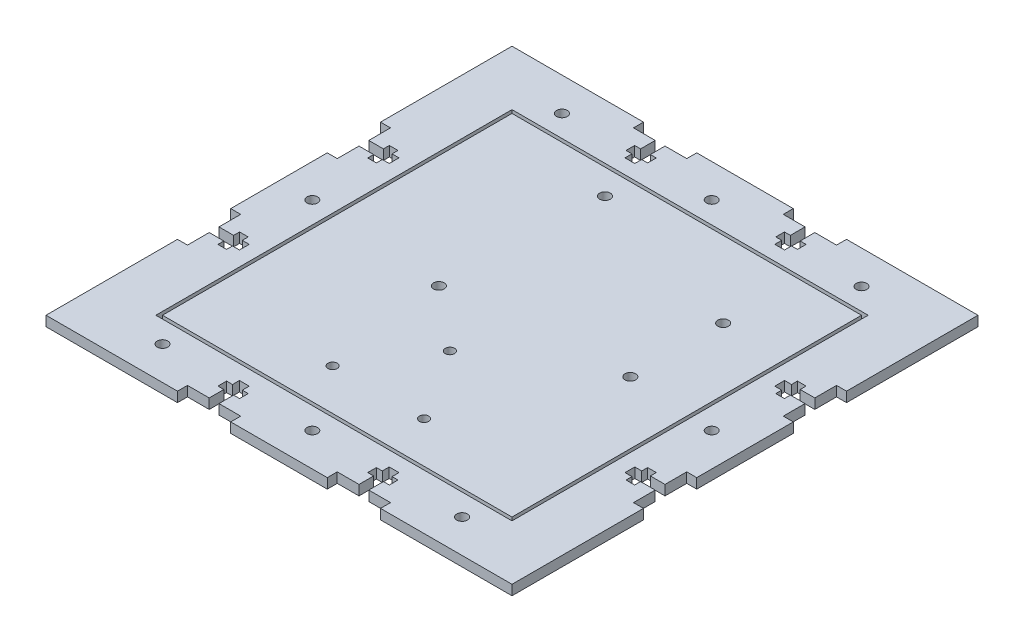
SolidWorks part; units mm, degrees
ref_plane "Front Plane" through (0, 0, 0) normal (0, 0, 1) x (1, 0, 0)
ref_plane "Top Plane" through (0, 0, 0) normal (0, 1, 0) x (1, 0, 0)
ref_plane "Right Plane" through (0, 0, 0) normal (1, 0, 0) x (0, 0, -1)
sketch "Sketch2" plane through (0, 0, 0) normal (0, 1, 0) x (1, 0, 0)
  line L0 (-70, 70) -> (70, -70) construction
  line L1 (-70, 70) -> (70, 70)
  line L2 (-70, 70) -> (-70, -70)
  line L3 (-70, -70) -> (70, -70)
  line L4 (70, 70) -> (70, -70)
  line L5 (70, 70) -> (-70, -70) construction
  line L6 (-0.0302, -29.4237) -> (-0.0302, -47.5058) construction
  line L7 (-50, 50) -> (50, -50) construction
  line L8 (50, 50) -> (-50, 50)
  line L9 (50, 50) -> (50, -50)
  line L10 (50, -50) -> (-50, -50)
  line L11 (-50, 50) -> (-50, -50)
  line L12 (50, 50) -> (-50, -50) construction
  line L13 (-18.6116, -3.3508) -> (-18.6116, 44.9492) construction
  line L14 (33.7884, 1.7492) -> (22.0917, 1.7492)
  line L15 (-18.6116, -3.3508) -> (22.0917, -3.3508)
  line L16 (22.0917, -3.3508) -> (22.0917, 1.7492)
  line L17 (0, 70) -> (0, -70) construction
  line L18 (-70, 0) -> (70, 0) construction
  line L19 (0, 70) -> (0, 50) construction
  line L20 (-50, 0) -> (-70, 0) construction
  line L21 (0, -50) -> (0, -70) construction
  line L22 (50, 0) -> (70, 0) construction
  line L23 (-45, 70) -> (-45, -70) construction
  line L24 (45, 70) -> (45, -70) construction
  line L25 (-45, 50) -> (-45, 70) construction
  line L26 (45, 50) -> (45, 70) construction
  line L27 (-45, -50) -> (-45, -70) construction
  line L28 (45, -50) -> (45, -70) construction
  circle A3 centre (-17.0116, 44.9492) radius 1.6
  circle A4 centre (-18.6116, -3.3508) radius 1.6
  circle A5 centre (33.7884, 29.6492) radius 1.6
  circle A6 centre (33.7884, 1.7492) radius 1.6
  circle A10 centre (0, 60) radius 1.6
  circle A11 centre (-60, 0) radius 1.6
  circle A12 centre (0, -60) radius 1.6
  circle A13 centre (60, 0) radius 1.6
  circle A14 centre (-45, 60) radius 1.6
  circle A15 centre (45, 60) radius 1.6
  circle A16 centre (-45, -60) radius 1.6
  circle A17 centre (45, -60) radius 1.6
  circle A18 centre (-0.0302, -18.6237) radius 1.4
  circle A19 centre (-13.7802, -40.1237) radius 1.4
  circle A20 centre (13.7198, -40.1237) radius 1.4
  point P12 (0, 0)
  point P18 (0, 0)
  point P40 (0, 60)
  point P44 (-60, 0)
  point P49 (0, -60)
  point P54 (60, 0)
  point P63 (-45, 60)
  point P68 (45, 60)
  point P73 (-45, -60)
  point P78 (45, -60)
  dimension "D3" = 25
  dimension "D9" = 3.2
  dimension "D11" = 2.8
  dimension "D1" = 140
  dimension "D2" = 100
  dimension "D4" = 50.8
  dimension "D5" = 27.9
  dimension "D6" = 5.1
  dimension "D7" = 48.3
  dimension "D8" = 40.7033
  dimension "D10" = 25
extrude "Boss-Extrude2" add sketch "Sketch2" along normal blind 3
sketch "Sketch3" plane through (0, 3, 0) normal (0, 1, 0) x (1, 0, 0)
  line L0 (-30.5, 70) -> (-30.5, 67)
  line L1 (-70, 70) -> (70, 70) construction
  line L2 (-30.5, 67) -> (-14.5, 67)
  line L3 (-14.5, 67) -> (-14.5, 70)
  line L4 (-14.5, 70) -> (-30.5, 70)
  line L6 (-1.65, 0) -> (1.65, 0) construction
  line L7 (-70, 70) -> (-70, -70) construction
  line L8 (-14.5, -67) -> (-14.5, -70)
  line L9 (-30.5, -67) -> (-14.5, -67)
  line L10 (-30.5, -70) -> (-30.5, -67)
  line L11 (-14.5, -70) -> (-30.5, -70)
  line L12 (0, -1.65) -> (0, 1.65) construction
  line L13 (30.5, -67) -> (14.5, -67)
  line L14 (30.5, -70) -> (30.5, -67)
  line L15 (14.5, -70) -> (30.5, -70)
  line L16 (14.5, -67) -> (14.5, -70)
  line L17 (14.5, 67) -> (14.5, 70)
  line L18 (30.5, 67) -> (14.5, 67)
  line L19 (30.5, 70) -> (30.5, 67)
  line L20 (14.5, 70) -> (30.5, 70)
  line L21 (-70, 30.5) -> (-67, 30.5)
  line L22 (-67, 30.5) -> (-67, 14.5)
  line L23 (-67, 14.5) -> (-70, 14.5)
  line L25 (-70, 14.5) -> (-70, 30.5)
  line L27 (67, 14.5) -> (70, 14.5)
  line L28 (67, 30.5) -> (67, 14.5)
  line L29 (70, 30.5) -> (67, 30.5)
  line L30 (70, 14.5) -> (70, 30.5)
  line L31 (67, -30.5) -> (67, -14.5)
  line L32 (70, -30.5) -> (67, -30.5)
  line L33 (70, -14.5) -> (70, -30.5)
  line L34 (67, -14.5) -> (70, -14.5)
  line L35 (-67, -14.5) -> (-70, -14.5)
  line L36 (-67, -30.5) -> (-67, -14.5)
  line L37 (-70, -30.5) -> (-67, -30.5)
  line L38 (-70, -14.5) -> (-70, -30.5)
  dimension "D3" = 39.5
  dimension "D1" = 3
  dimension "D2" = 16
  dimension "D4" = 3
  dimension "D5" = 16
  dimension "D6" = 39.5
extrude "Cut-Extrude2" cut sketch "Sketch3" against normal blind 3
sketch "Sketch4" plane through (0, 3, 0) normal (0, 1, 0) x (1, 0, 0)
  line L0 (-22.5, 67) -> (-22.5, -67) construction
  line L1 (-30.5, 67) -> (-14.5, 67) construction
  line L2 (-14.5, -67) -> (-30.5, -67) construction
  line L3 (-23.97, 67) -> (-23.97, 62.6)
  line L4 (-67, 22.5) -> (67, 22.5) construction
  line L5 (-67, 14.5) -> (-67, 30.5) construction
  line L6 (-23.97, 62.6) -> (-25.75, 62.6)
  line L7 (67, 30.5) -> (67, 14.5) construction
  line L9 (-25.75, 62.6) -> (-25.75, 60)
  line L10 (-25.75, 60) -> (-23.97, 60)
  line L11 (-23.97, 60) -> (-23.97, 57.92)
  line L12 (-23.97, 57.92) -> (-21.03, 57.92)
  line L14 (-21.03, 67) -> (-23.97, 67)
  line L15 (-21.03, 60) -> (-21.03, 57.92)
  line L16 (-19.25, 60) -> (-21.03, 60)
  line L17 (-19.25, 62.6) -> (-19.25, 60)
  line L18 (-21.03, 62.6) -> (-19.25, 62.6)
  line L19 (-21.03, 67) -> (-21.03, 62.6)
  line L20 (-1.65, 0) -> (1.65, 0) construction
  line L21 (-23.97, -62.6) -> (-25.75, -62.6)
  line L22 (-23.97, -67) -> (-23.97, -62.6)
  line L23 (-21.03, -67) -> (-23.97, -67)
  line L24 (-21.03, -67) -> (-21.03, -62.6)
  line L25 (-21.03, -62.6) -> (-19.25, -62.6)
  line L26 (-19.25, -62.6) -> (-19.25, -60)
  line L27 (-19.25, -60) -> (-21.03, -60)
  line L28 (-21.03, -60) -> (-21.03, -57.92)
  line L29 (-23.97, -57.92) -> (-21.03, -57.92)
  line L30 (-23.97, -60) -> (-23.97, -57.92)
  line L31 (-25.75, -60) -> (-23.97, -60)
  line L32 (-25.75, -62.6) -> (-25.75, -60)
  line L33 (0, -1.65) -> (0, 1.65) construction
  line L34 (21.03, -60) -> (21.03, -57.92)
  line L35 (21.03, -67) -> (23.97, -67)
  line L36 (23.97, -67) -> (23.97, -62.6)
  line L37 (23.97, -62.6) -> (25.75, -62.6)
  line L38 (25.75, -62.6) -> (25.75, -60)
  line L39 (25.75, -60) -> (23.97, -60)
  line L40 (23.97, -60) -> (23.97, -57.92)
  line L41 (23.97, -57.92) -> (21.03, -57.92)
  line L42 (19.25, -60) -> (21.03, -60)
  line L43 (19.25, -62.6) -> (19.25, -60)
  line L44 (21.03, -62.6) -> (19.25, -62.6)
  line L45 (21.03, -67) -> (21.03, -62.6)
  line L46 (21.03, 67) -> (23.97, 67)
  line L47 (21.03, 67) -> (21.03, 62.6)
  line L48 (21.03, 62.6) -> (19.25, 62.6)
  line L49 (23.97, 67) -> (23.97, 62.6)
  line L50 (23.97, 62.6) -> (25.75, 62.6)
  line L51 (25.75, 62.6) -> (25.75, 60)
  line L52 (25.75, 60) -> (23.97, 60)
  line L53 (23.97, 60) -> (23.97, 57.92)
  line L54 (23.97, 57.92) -> (21.03, 57.92)
  line L55 (21.03, 60) -> (21.03, 57.92)
  line L56 (19.25, 60) -> (21.03, 60)
  line L57 (19.25, 62.6) -> (19.25, 60)
  line L76 (67, 23.97) -> (62.6, 23.97)
  line L77 (62.6, 23.97) -> (62.6, 25.75)
  line L90 (67, 23.97) -> (67, 21.03)
  line L91 (67, 21.03) -> (62.6, 21.03)
  line L92 (62.6, 21.03) -> (62.6, 19.25)
  line L93 (62.6, 19.25) -> (60, 19.25)
  line L94 (60, 19.25) -> (60, 21.03)
  line L95 (60, 21.03) -> (57.92, 21.03)
  line L96 (57.92, 21.03) -> (57.92, 23.97)
  line L97 (62.6, 25.75) -> (60, 25.75)
  line L98 (60, 25.75) -> (60, 23.97)
  line L99 (60, 23.97) -> (57.92, 23.97)
  line L100 (-67, 23.97) -> (-67, 21.03)
  line L101 (-67, 23.97) -> (-62.6, 23.97)
  line L102 (-62.6, 23.97) -> (-62.6, 25.75)
  line L103 (-62.6, 25.75) -> (-60, 25.75)
  line L104 (-60, 25.75) -> (-60, 23.97)
  line L105 (-60, 23.97) -> (-57.92, 23.97)
  line L106 (-57.92, 21.03) -> (-57.92, 23.97)
  line L107 (-60, 21.03) -> (-57.92, 21.03)
  line L108 (-60, 19.25) -> (-60, 21.03)
  line L109 (-62.6, 19.25) -> (-60, 19.25)
  line L110 (-62.6, 21.03) -> (-62.6, 19.25)
  line L111 (-67, 21.03) -> (-62.6, 21.03)
  line L112 (-67, -23.97) -> (-62.6, -23.97)
  line L113 (-62.6, -23.97) -> (-62.6, -25.75)
  line L114 (-62.6, -25.75) -> (-60, -25.75)
  line L115 (-60, -25.75) -> (-60, -23.97)
  line L116 (-60, -23.97) -> (-57.92, -23.97)
  line L117 (-57.92, -21.03) -> (-57.92, -23.97)
  line L118 (-60, -21.03) -> (-57.92, -21.03)
  line L119 (-60, -19.25) -> (-60, -21.03)
  line L120 (-62.6, -19.25) -> (-60, -19.25)
  line L121 (-62.6, -21.03) -> (-62.6, -19.25)
  line L122 (-67, -21.03) -> (-62.6, -21.03)
  line L123 (-67, -23.97) -> (-67, -21.03)
  line L124 (67, -23.97) -> (62.6, -23.97)
  line L125 (62.6, -23.97) -> (62.6, -25.75)
  line L126 (62.6, -25.75) -> (60, -25.75)
  line L127 (60, -25.75) -> (60, -23.97)
  line L128 (60, -23.97) -> (57.92, -23.97)
  line L129 (57.92, -21.03) -> (57.92, -23.97)
  line L130 (60, -21.03) -> (57.92, -21.03)
  line L131 (60, -19.25) -> (60, -21.03)
  line L132 (62.6, -19.25) -> (60, -19.25)
  line L133 (62.6, -21.03) -> (62.6, -19.25)
  line L134 (67, -21.03) -> (62.6, -21.03)
  line L135 (67, -23.97) -> (67, -21.03)
  point P15 (-22.5, 57.92)
  point P79 (57.92, 22.5)
  dimension "D1" = 4.4
  dimension "D2" = 2.6
  dimension "D3" = 2.94
  dimension "D4" = 1.78
  dimension "D5" = 2.08
  dimension "D6" = 1.78
  dimension "D7" = 2.08
  dimension "D8" = 2.6
  dimension "D9" = 4.4
  dimension "D10" = 2.94
extrude "Cut-Extrude3" cut sketch "Sketch4" against normal blind 3
sketch "Sketch5" plane through (0, 3, 0) normal (0, 1, 0) x (1, 0, 0)
  line L0 (53.5, 53.5) -> (53.5, -53.5)
  line L1 (52.5, 52.5) -> (-52.5, 52.5)
  line L2 (52.5, 52.5) -> (52.5, -52.5)
  line L3 (52.5, -52.5) -> (-52.5, -52.5)
  line L4 (-52.5, 52.5) -> (-52.5, -52.5)
  line L5 (52.5, 52.5) -> (-52.5, -52.5) construction
  line L6 (52.5, -52.5) -> (-52.5, 52.5) construction
  line L7 (53.5, -53.5) -> (-53.5, -53.5)
  line L8 (-53.5, 53.5) -> (-53.5, -53.5)
  line L9 (53.5, 53.5) -> (-53.5, 53.5)
  point P0 (0, 0)
  dimension "D1" = 105
  dimension "D2" = 1
extrude "Cut-Extrude5" cut sketch "Sketch5" against normal blind 3
